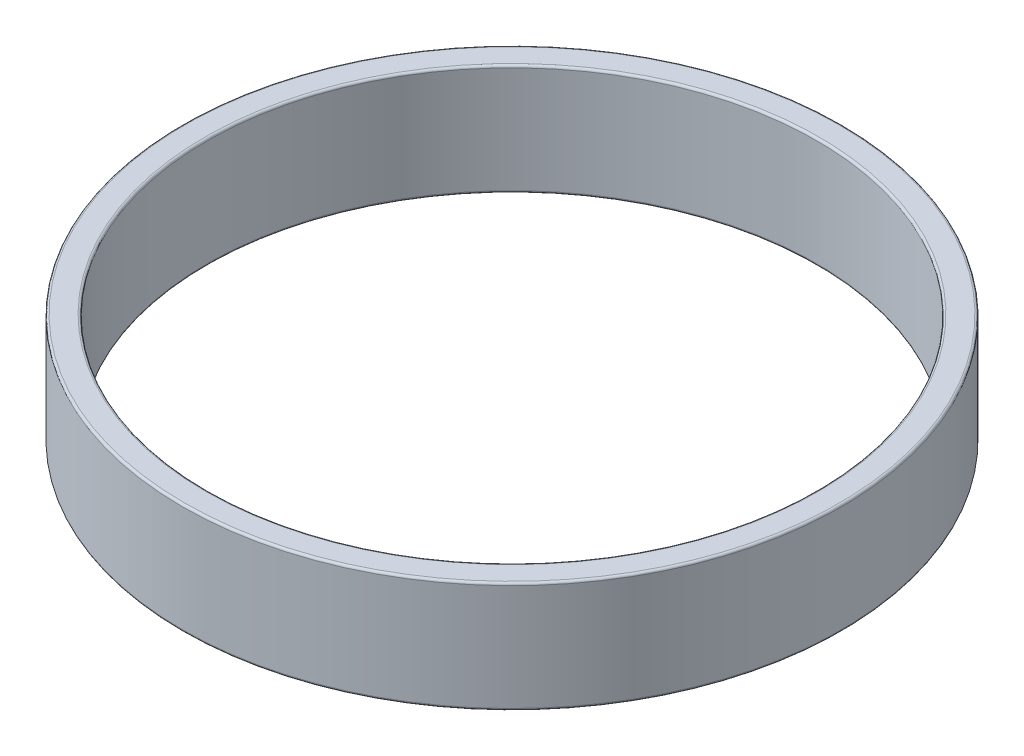
SolidWorks part; units mm, degrees
ref_plane "Front Plane" through (0, 0, 0) normal (0, 0, 1) x (1, 0, 0)
ref_plane "Top Plane" through (0, 0, 0) normal (0, 1, 0) x (1, 0, 0)
ref_plane "Right Plane" through (0, 0, 0) normal (1, 0, 0) x (0, 0, -1)
sketch "Sketch1" plane through (0, 0, 0) normal (0, 1, 0) x (1, 0, 0)
  circle A0 centre (0, 0) radius 69.85
  circle A1 centre (0, 0) radius 75.565
  dimension "D1" = 151.13
  dimension "D2" = 139.7
extrude "Boss-Extrude1" add sketch "Sketch1" along normal blind 25.4
fillet "Fillet1" radius 0.508 4 edges at (0, 0, 69.85) (0, 25.4, 69.85) (0, 0, 75.565) (0, 25.4, 75.565)
